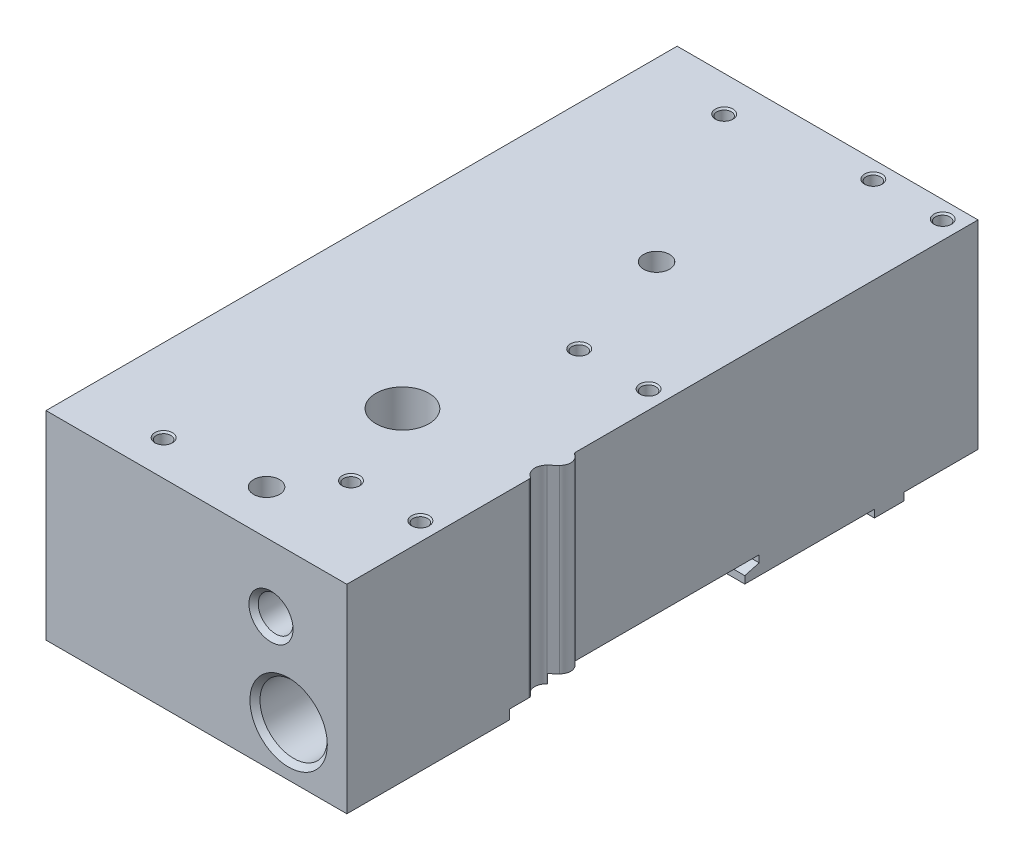
SolidWorks part; units mm, degrees
ref_plane "Front Plane" through (0, 0, 0) normal (0, 0, 1) x (1, 0, 0)
ref_plane "Top Plane" through (0, 0, 0) normal (0, 1, 0) x (1, 0, 0)
ref_plane "Right Plane" through (0, 0, 0) normal (1, 0, 0) x (0, 0, -1)
ref_plane "Plane1" through (0, 1.3, 0) normal (0, 1, 0) x (1, 0, 0)
sketch "Sketch1" plane through (0, 1.3, 0) normal (0, 1, 0) x (1, 0, 0)
  line L0 (-12.75, -53.65) -> (38.4, -53.65)
  line L1 (38.4, -53.65) -> (38.4, -22.6542)
  line L2 (37.8839, -19.0892) -> (38.9795, -18.0647)
  line L3 (38.4, -14.7581) -> (38.4, 53.65)
  line L4 (38.4, 53.65) -> (-12.75, 53.65)
  line L5 (-12.75, 53.65) -> (-12.75, -53.65)
  arc A0 (38.4, -22.6542) -> (38.17, -22.2333) centre (37.9, -22.6542) ccw
  arc A1 (38.17, -22.2333) -> (37.8839, -19.0892) centre (39.25, -20.55) cw
  arc A2 (38.9795, -18.0647) -> (38.65, -15.1912) centre (37.75, -16.75) ccw
  arc A3 (38.65, -15.1912) -> (38.4, -14.7581) centre (38.9, -14.7581) cw
extrude "Boss-Extrude1" add sketch "Sketch1" along normal blind 33.8
ref_plane "Plane2" through (0, 0, 0) normal (1, 0, 0) x (0, 0, -1)
sketch "Sketch2" plane through (0, 0, 0) normal (1, 0, 0) x (0, 0, -1)
  line L0 (-26, 2.9) -> (-26, -8.1744)
  line L1 (-26, -8.1744) -> (14, -7.9637)
  line L2 (14, -7.9637) -> (14, 2.5435)
  line L3 (14, 2.5435) -> (16.45, 3.2)
  line L4 (16.45, 3.2) -> (16.45, 4.4)
  line L5 (16.45, 4.4) -> (-19.05, 4.4)
  line L6 (-19.05, 4.4) -> (-19.05, 2.9)
  line L7 (-19.05, 2.9) -> (-26, 2.9)
extrude "Cut-Extrude1" cut sketch "Sketch2" against normal blind 40 and the other way blind 40
ref_plane "Plane3" through (28.5, 0, 0) normal (1, 0, 0) x (0, 0, -1)
sketch "Sketch3" plane through (28.5, 0, 0) normal (1, 0, 0) x (0, 0, -1)
  line L0 (-53.65, 9.8) -> (-53.65, 16.3785)
  line L1 (-53.65, 16.3785) -> (-52.794, 15.5225)
  line L2 (-52.794, 15.5225) -> (-35.65, 15.5225)
  line L3 (-35.65, 15.5225) -> (-35.65, 9.8)
  line L4 (-35.65, 9.8) -> (-53.65, 9.8)
  line L5 (-35.65, 9.8) -> (-53.65, 9.8) construction
revolve "Cut-Revolve1" cut sketch "Sketch3" angle 360 about L5
cosmetic thread "Cosmetic Thread1" parameters "D1"=18, "D2"=13.157
ref_plane "Plane4" through (25.5, 0, 0) normal (1, 0, 0) x (0, 0, -1)
sketch "Sketch4" plane through (25.5, 0, 0) normal (1, 0, 0) x (0, 0, -1)
  line L0 (-53.65, 23.9) -> (-53.65, 27.65)
  line L1 (-53.65, 27.65) -> (-52.86, 26.86)
  line L2 (-52.86, 26.86) -> (-44.65, 26.86)
  line L3 (-44.65, 26.86) -> (-44.65, 23.9)
  line L4 (-44.65, 23.9) -> (-53.65, 23.9)
  line L5 (-44.65, 23.9) -> (-53.65, 23.9) construction
revolve "Cut-Revolve2" cut sketch "Sketch4" angle 360 about L5
ref_plane "Plane5" through (1.25, 0, 0) normal (1, 0, 0) x (0, 0, -1)
sketch "Sketch5" plane through (1.25, 0, 0) normal (1, 0, 0) x (0, 0, -1)
  line L0 (47.65, 35.1) -> (49.15, 35.1)
  line L1 (49.15, 35.1) -> (48.8795, 34.8295)
  line L2 (48.8795, 34.8295) -> (48.8795, 30.1)
  line L3 (48.8795, 30.1) -> (47.65, 30.1)
  line L4 (47.65, 30.1) -> (47.65, 35.1)
  line L5 (47.65, 30.1) -> (47.65, 35.1) construction
revolve "Cut-Revolve3" cut sketch "Sketch5" angle 360 about L5
cosmetic thread "Cosmetic Thread2" parameters "D1"=5, "D2"=3
ref_plane "Plane6" through (1.25, 0, 0) normal (1, 0, 0) x (0, 0, -1)
sketch "Sketch6" plane through (1.25, 0, 0) normal (1, 0, 0) x (0, 0, -1)
  line L0 (-47.65, 35.1) -> (-46.15, 35.1)
  line L1 (-46.15, 35.1) -> (-46.4205, 34.8295)
  line L2 (-46.4205, 34.8295) -> (-46.4205, 30.1)
  line L3 (-46.4205, 30.1) -> (-47.65, 30.1)
  line L4 (-47.65, 30.1) -> (-47.65, 35.1)
  line L5 (-47.65, 30.1) -> (-47.65, 35.1) construction
revolve "Cut-Revolve4" cut sketch "Sketch6" angle 360 about L5
cosmetic thread "Cosmetic Thread3" parameters "D1"=5, "D2"=3
ref_plane "Plane7" through (23.5, 0, 0) normal (1, 0, 0) x (0, 0, -1)
sketch "Sketch7" plane through (23.5, 0, 0) normal (1, 0, 0) x (0, 0, -1)
  line L0 (-38.05, 35.1) -> (-36.55, 35.1)
  line L1 (-36.55, 35.1) -> (-36.8205, 34.8295)
  line L2 (-36.8205, 34.8295) -> (-36.8205, 30.1)
  line L3 (-36.8205, 30.1) -> (-38.05, 30.1)
  line L4 (-38.05, 30.1) -> (-38.05, 35.1)
  line L5 (-38.05, 30.1) -> (-38.05, 35.1) construction
revolve "Cut-Revolve5" cut sketch "Sketch7" angle 360 about L5
cosmetic thread "Cosmetic Thread4" parameters "D1"=5, "D2"=3
ref_plane "Plane8" through (23.5, 0, 0) normal (1, 0, 0) x (0, 0, -1)
sketch "Sketch8" plane through (23.5, 0, 0) normal (1, 0, 0) x (0, 0, -1)
  line L0 (0.75, 35.1) -> (2.25, 35.1)
  line L1 (2.25, 35.1) -> (1.9795, 34.8295)
  line L2 (1.9795, 34.8295) -> (1.9795, 30.1)
  line L3 (1.9795, 30.1) -> (0.75, 30.1)
  line L4 (0.75, 30.1) -> (0.75, 35.1)
  line L5 (0.75, 30.1) -> (0.75, 35.1) construction
revolve "Cut-Revolve6" cut sketch "Sketch8" angle 360 about L5
cosmetic thread "Cosmetic Thread5" parameters "D1"=5, "D2"=3
ref_plane "Plane9" through (23.5, 0, 0) normal (1, 0, 0) x (0, 0, -1)
sketch "Sketch9" plane through (23.5, 0, 0) normal (1, 0, 0) x (0, 0, -1)
  line L0 (50.75, 35.1) -> (52.25, 35.1)
  line L1 (52.25, 35.1) -> (51.9795, 34.8295)
  line L2 (51.9795, 34.8295) -> (51.9795, 30.1)
  line L3 (51.9795, 30.1) -> (50.75, 30.1)
  line L4 (50.75, 30.1) -> (50.75, 35.1)
  line L5 (50.75, 30.1) -> (50.75, 35.1) construction
revolve "Cut-Revolve7" cut sketch "Sketch9" angle 360 about L5
cosmetic thread "Cosmetic Thread6" parameters "D1"=5, "D2"=3
ref_plane "Plane10" through (35.3, 0, 0) normal (1, 0, 0) x (0, 0, -1)
sketch "Sketch10" plane through (35.3, 0, 0) normal (1, 0, 0) x (0, 0, -1)
  line L0 (-38.05, 35.1) -> (-36.55, 35.1)
  line L1 (-36.55, 35.1) -> (-36.8205, 34.8295)
  line L2 (-36.8205, 34.8295) -> (-36.8205, 30.1)
  line L3 (-36.8205, 30.1) -> (-38.05, 30.1)
  line L4 (-38.05, 30.1) -> (-38.05, 35.1)
  line L5 (-38.05, 30.1) -> (-38.05, 35.1) construction
revolve "Cut-Revolve8" cut sketch "Sketch10" angle 360 about L5
cosmetic thread "Cosmetic Thread7" parameters "D1"=5, "D2"=3
ref_plane "Plane11" through (35.3, 0, 0) normal (1, 0, 0) x (0, 0, -1)
sketch "Sketch11" plane through (35.3, 0, 0) normal (1, 0, 0) x (0, 0, -1)
  line L0 (0.75, 35.1) -> (2.25, 35.1)
  line L1 (2.25, 35.1) -> (1.9795, 34.8295)
  line L2 (1.9795, 34.8295) -> (1.9795, 30.1)
  line L3 (1.9795, 30.1) -> (0.75, 30.1)
  line L4 (0.75, 30.1) -> (0.75, 35.1)
  line L5 (0.75, 30.1) -> (0.75, 35.1) construction
revolve "Cut-Revolve9" cut sketch "Sketch11" angle 360 about L5
cosmetic thread "Cosmetic Thread8" parameters "D1"=5, "D2"=3
ref_plane "Plane12" through (35.3, 0, 0) normal (1, 0, 0) x (0, 0, -1)
sketch "Sketch12" plane through (35.3, 0, 0) normal (1, 0, 0) x (0, 0, -1)
  line L0 (50.75, 35.1) -> (52.25, 35.1)
  line L1 (52.25, 35.1) -> (51.9795, 34.8295)
  line L2 (51.9795, 34.8295) -> (51.9795, 30.1)
  line L3 (51.9795, 30.1) -> (50.75, 30.1)
  line L4 (50.75, 30.1) -> (50.75, 35.1)
  line L5 (50.75, 30.1) -> (50.75, 35.1) construction
revolve "Cut-Revolve10" cut sketch "Sketch12" angle 360 about L5
cosmetic thread "Cosmetic Thread9" parameters "D1"=5, "D2"=3
ref_plane "Plane13" through (0, 1.3, 0) normal (0, -1, 0) x (-1, 0, 0)
sketch "Sketch13" plane through (0, 1.3, 0) normal (0, -1, 0) x (-1, 0, 0)
  circle A0 centre (-17.65, -46.15) radius 4
extrude "Boss-Extrude2" add sketch "Sketch13" along normal blind 1.3
ref_plane "Plane14" through (0, 1.3, 0) normal (0, -1, 0) x (-1, 0, 0)
sketch "Sketch14" plane through (0, 1.3, 0) normal (0, -1, 0) x (-1, 0, 0)
  circle A0 centre (-17.65, 20.15) radius 4
extrude "Boss-Extrude3" add sketch "Sketch14" along normal blind 1.3
ref_plane "Plane15" through (17.25, 0, 0) normal (1, 0, 0) x (0, 0, -1)
sketch "Sketch15" plane through (17.25, 0, 0) normal (1, 0, 0) x (0, 0, -1)
  line L0 (-46.15, 35.1) -> (-43.95, 35.1)
  line L1 (-43.95, 35.1) -> (-43.95, 0)
  line L2 (-43.95, 0) -> (-46.15, 0)
  line L3 (-46.15, 0) -> (-46.15, 35.1)
  line L4 (-46.15, 0) -> (-46.15, 35.1) construction
revolve "Cut-Revolve11" cut sketch "Sketch15" angle 360 about L4
ref_plane "Plane16" through (17.25, 0, 0) normal (1, 0, 0) x (0, 0, -1)
sketch "Sketch16" plane through (17.25, 0, 0) normal (1, 0, 0) x (0, 0, -1)
  line L0 (-23.05, 35.1) -> (-18.55, 35.1)
  line L1 (-18.55, 35.1) -> (-18.55, 10.1)
  line L2 (-18.55, 10.1) -> (-20.85, 10.1)
  line L3 (-20.85, 10.1) -> (-20.85, 0)
  line L4 (-20.85, 0) -> (-23.05, 0)
  line L5 (-23.05, 0) -> (-23.05, 35.1)
  line L6 (-23.05, 0) -> (-23.05, 35.1) construction
revolve "Cut-Revolve12" cut sketch "Sketch16" angle 360 about L6
ref_plane "Plane17" through (17.25, 0, 0) normal (1, 0, 0) x (0, 0, -1)
sketch "Sketch17" plane through (17.25, 0, 0) normal (1, 0, 0) x (0, 0, -1)
  line L0 (20.15, 35.1) -> (22.35, 35.1)
  line L1 (22.35, 35.1) -> (22.35, 0)
  line L2 (22.35, 0) -> (20.15, 0)
  line L3 (20.15, 0) -> (20.15, 35.1)
  line L4 (20.15, 0) -> (20.15, 35.1) construction
revolve "Cut-Revolve13" cut sketch "Sketch17" angle 360 about L4
ref_plane "Plane18" through (0, 0, 0) normal (0, 1, 0) x (1, 0, 0)
sketch "Sketch18" plane through (0, 0, 0) normal (0, 1, 0) x (1, 0, 0)
  line L0 (35.9, 36.05) -> (38.4, 36.05)
  line L1 (38.4, 36.05) -> (38.4, 41.05)
  line L2 (38.4, 41.05) -> (35.9, 41.05)
  line L3 (35.9, 41.05) -> (35.9, 36.05)
extrude "Boss-Extrude4" add sketch "Sketch18" along normal blind 1.5
ref_plane "Plane19" through (0, 0, 0) normal (0, 1, 0) x (1, 0, 0)
sketch "Sketch19" plane through (0, 0, 0) normal (0, 1, 0) x (1, 0, 0)
  line L0 (-4.65, 36.05) -> (-2.65, 36.05)
  line L1 (-2.65, 36.05) -> (-2.65, 41.05)
  line L2 (-2.65, 41.05) -> (-4.65, 41.05)
  line L3 (-4.65, 41.05) -> (-4.65, 36.05)
extrude "Boss-Extrude5" add sketch "Sketch19" along normal blind 1.5
